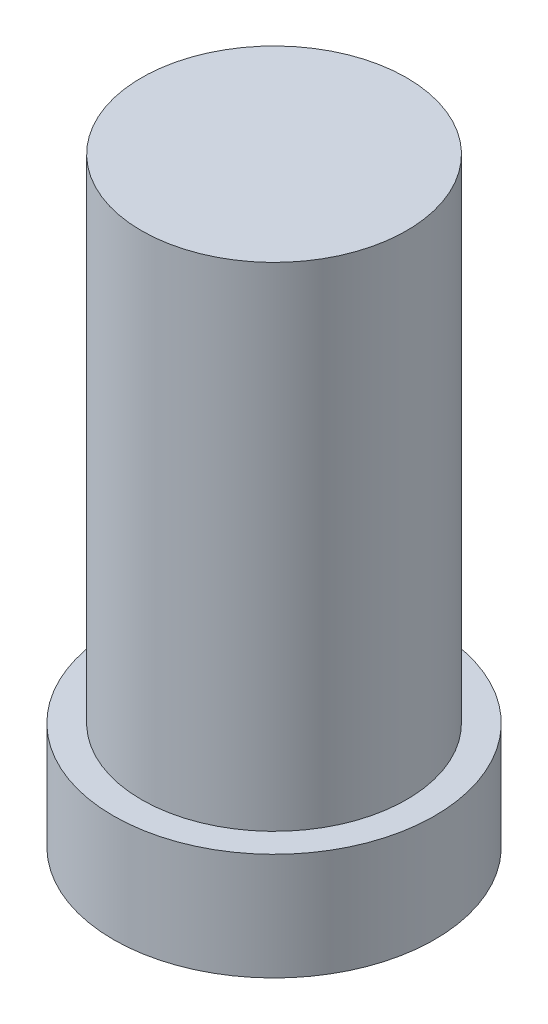
SolidWorks part; units mm, degrees
ref_plane "Front Plane" through (0, 0, 0) normal (0, 0, 1) x (1, 0, 0)
ref_plane "Top Plane" through (0, 0, 0) normal (0, 1, 0) x (1, 0, 0)
ref_plane "Right Plane" through (0, 0, 0) normal (1, 0, 0) x (0, 0, -1)
sketch "Sketch3" plane through (0, 0, 0) normal (0, 1, 0) x (1, 0, 0)
  circle A0 centre (0, 0) radius 3
extrude "Boss-Extrude1" add sketch "Sketch3" along normal blind 2
sketch "Sketch4" plane through (0, 0, 0) normal (0, 1, 0) x (1, 0, 0)
  line L0 (0, -1.1) -> (0, 1.1) construction
  circle A0 centre (0, 0) radius 2.475
  circle A1 centre (0, 0) radius 3 construction
  dimension "D1" = 4.95
extrude "Boss-Extrude2" add sketch "Sketch4" along normal blind 11.2
